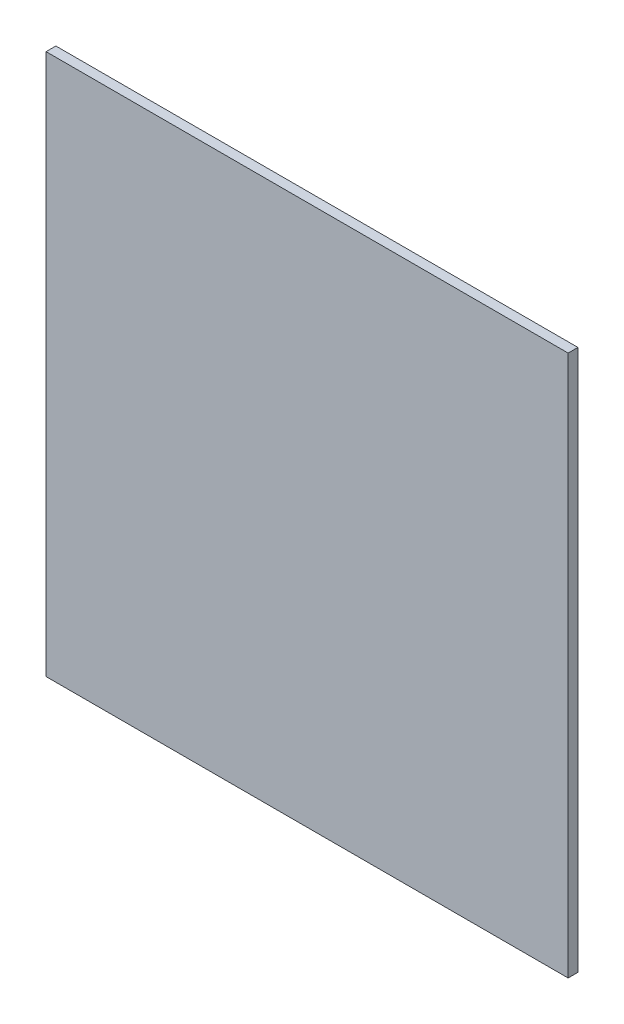
SolidWorks part; units mm, degrees
ref_plane "Front Plane" through (0, 0, 0) normal (0, 0, 1) x (1, 0, 0)
ref_plane "Top Plane" through (0, 0, 0) normal (0, 1, 0) x (1, 0, 0)
ref_plane "Right Plane" through (0, 0, 0) normal (1, 0, 0) x (0, 0, -1)
sketch "Sketch1" plane through (0, 0, 0) normal (0, 0, 1) x (1, 0, 0)
  line L0 (-30, -41.4693) -> (-40, -41.4693)
  line L1 (-40, 41.4693) -> (40, 41.4693)
  line L2 (-40, 41.4693) -> (-40, -31.102)
  line L3 (-30, -41.4693) -> (40, -41.4693)
  line L4 (40, 41.4693) -> (40, -41.4693)
  line L5 (-40, 41.4693) -> (40, -41.4693) construction
  line L6 (0, 0) -> (40, 41.4693) construction
  line L11 (-40, -41.4693) -> (-40, -31.102)
  point P0 (0, 0)
  dimension "D2" = 82.9386
extrude "Boss-Extrude1" add sketch "Sketch1" along normal blind 1.5
